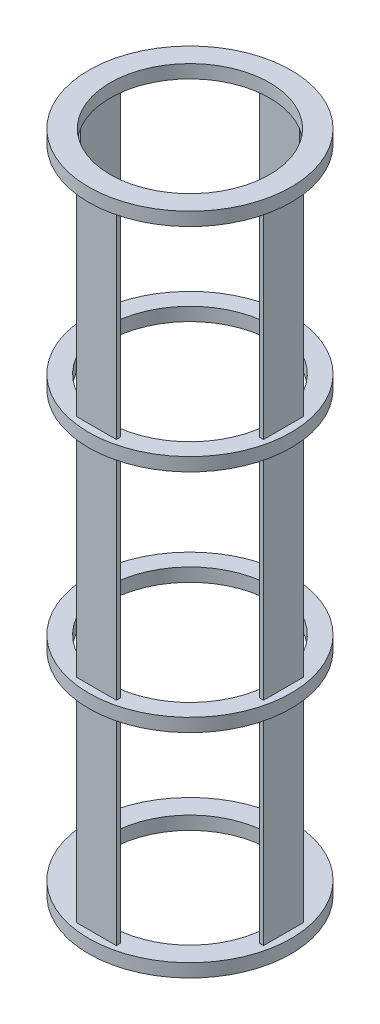
SolidWorks part; units mm, degrees
ref_plane "Plan de face" through (0, 0, 0) normal (0, 0, 1) x (1, 0, 0)
ref_plane "Plan de dessus" through (0, 0, 0) normal (0, 1, 0) x (1, 0, 0)
ref_plane "Plan de droite" through (0, 0, 0) normal (1, 0, 0) x (0, 0, -1)
sketch "Esquisse1" plane through (0, 0, 0) normal (0, 1, 0) x (1, 0, 0)
  circle A0 centre (0, 0) radius 76.2
  circle A1 centre (0, 0) radius 60
  dimension "D1" = 152.4
  dimension "D2" = 120
extrude "Boss.-Extru.1" add sketch "Esquisse1" along normal blind 10
sketch "Esquisse2" plane through (0, 10, 0) normal (0, 1, 0) x (1, 0, 0)
  line L0 (-15, 70.4202) -> (15, 70.4202)
  line L1 (15, 70.4202) -> (15, 67.4202)
  line L2 (15, 67.4202) -> (-15, 67.4202)
  line L3 (-15, 67.4202) -> (-15, 70.4202)
  line L4 (0, 67.4202) -> (0, 0) construction
  circle A0 centre (0, 0) radius 76.2 construction
  dimension "D1" = 30
  dimension "D2" = 72
  dimension "D3" = 3
extrude "Boss.-Extru.2" add sketch "Esquisse2" along normal blind 480
pattern_circular "Répétition circulaire1" count 4 over 360 about axis through (0, 0, 0) along (0, 1, 0) of "Boss.-Extru.2"
pattern_linear "Répétition linéaire1" count 2 spacing 490 along (0, 1, 0) of "Boss.-Extru.1"
ref_plane "Plan1" through (0, 160, 0) normal (0, 1, 0) x (1, 0, 0)
sketch "Esquisse5" plane through (0, 160, 0) normal (0, 1, 0) x (1, 0, 0)
  circle A0 centre (0, 0) radius 62.5
  circle A1 centre (0, 0) radius 76.2
  dimension "D1" = 125
extrude "Boss.-Extru.3" add sketch "Esquisse5" along normal blind 10
pattern_linear "Répétition linéaire2" count 2 spacing 170 along (0, 1, 0) of "Boss.-Extru.3"
equation "\"A\"=10"
